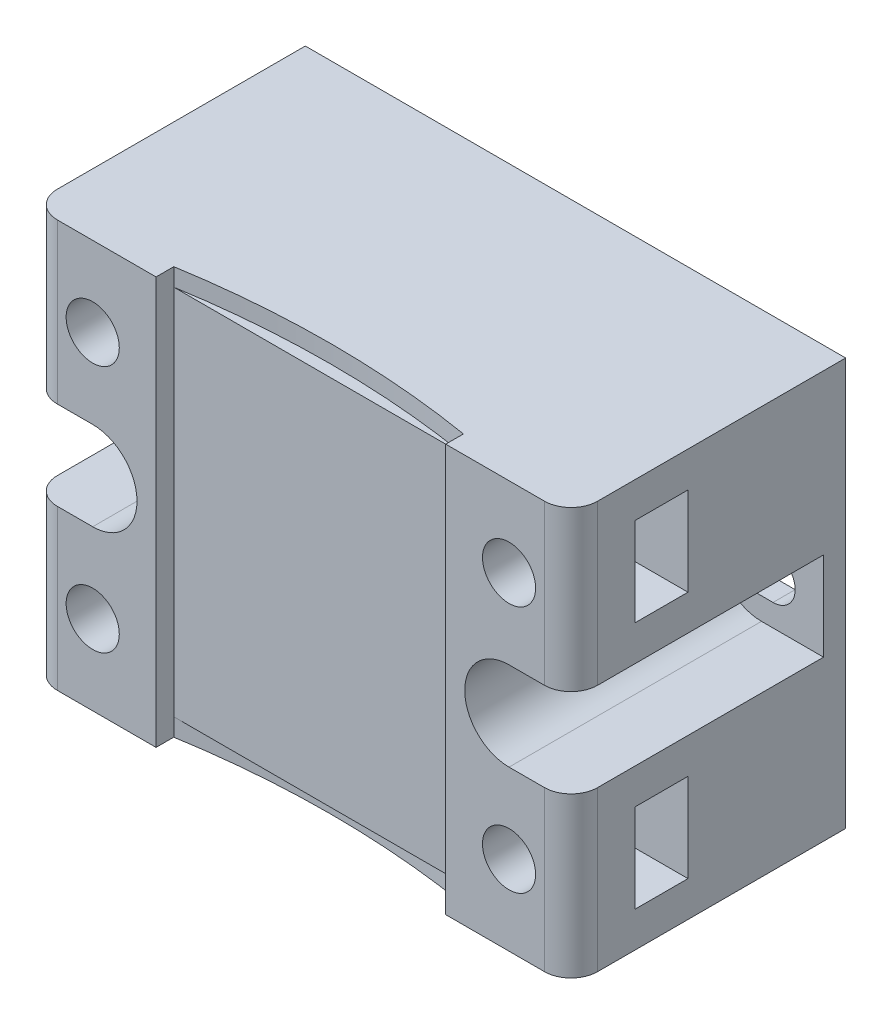
SolidWorks part; units mm, degrees
ref_plane "前视基准面" through (0, 0, 0) normal (0, 0, 1) x (1, 0, 0)
ref_plane "上视基准面" through (0, 0, 0) normal (0, 1, 0) x (1, 0, 0)
ref_plane "右视基准面" through (0, 0, 0) normal (1, 0, 0) x (0, 0, -1)
sketch "草图1" plane through (0, 0, 0) normal (0, 0, 1) x (1, 0, 0)
  line L1 (0, 0) -> (61, 0)
  line L2 (0, 0) -> (0, 46)
  line L3 (0, 46) -> (61, 46)
  line L4 (61, 0) -> (61, 46)
extrude "凸台-拉伸1" add sketch "草图1" along normal blind 31
sketch "草图2" plane through (0, 0, 31) normal (0, 0, 1) x (1, 0, 0)
  line L0 (30.5, 46) -> (30.5, 0)
  line L1 (61, 46) -> (0, 46) construction
  line L2 (0, 0) -> (61, 0) construction
  line L3 (30.5, 23) -> (12, 23)
  line L4 (12, 23) -> (7, 23)
  line L5 (7, 28) -> (0, 28)
  line L6 (0, 46) -> (61, 46)
  line L7 (0, 46) -> (0, 0)
  line L8 (0, 0) -> (61, 0)
  line L9 (61, 46) -> (61, 0)
  line L10 (0, 28) -> (0, 18)
  line L11 (0, 18) -> (7, 18)
  line L12 (61, 18) -> (54, 18)
  line L13 (54, 28) -> (61, 28)
  circle A0 centre (7, 23) radius 5
  circle A1 centre (54, 23) radius 5
  dimension "D1" = 10
extrude "切除-拉伸1" cut sketch "草图2" against normal blind 28.5
sketch "草图3" plane through (0, 0, 2.5) normal (0, 0, 1) x (1, 0, 0)
  line L0 (0, 23) -> (5.7, 23)
  line L1 (0, 28) -> (0, 18) construction
  circle A0 centre (5.7, 23) radius 2.5
  dimension "D1" = 5
extrude "切除-拉伸2" cut sketch "草图3" against normal blind 28.5
sketch "草图4" plane through (0, 0, 2.5) normal (0, 0, 1) x (1, 0, 0)
  line L3 (53.3, 25.5) -> (55.3, 25.5)
  line L4 (53.3, 20.5) -> (55.3, 20.5)
  arc A0 (55.3, 20.5) -> (55.3, 25.5) centre (55.3, 23) ccw
  arc A1 (53.3, 25.5) -> (53.3, 20.5) centre (53.3, 23) ccw
  dimension "D1" = 5
  dimension "D2" = 5
extrude "切除-拉伸3" cut sketch "草图4" against normal blind 28.5
sketch "草图5" plane through (0, 0, 0) normal (0, -1, 0) x (1, 0, 0)
  line L0 (30.5, 31) -> (46.85, 31)
  line L1 (0, 31) -> (61, 31) construction
  line L2 (46.85, 31) -> (46.85, 29)
  line L3 (46.85, 29) -> (14.15, 29)
  line L4 (14.15, 29) -> (14.15, 31)
  line L5 (14.15, 31) -> (30.5, 31)
extrude "切除-拉伸4" cut sketch "草图5" against normal blind 68.5
sketch "草图6" plane through (0, 0, 0) normal (0, -1, 0) x (1, 0, 0)
  line L0 (14.15, 29) -> (46.85, 29)
  arc A0 (14.15, 29) -> (46.85, 29) centre (30.5, 127.6543) ccw
extrude "切除-拉伸5" cut sketch "草图6" against normal blind 2
sketch "草图7" plane through (0, 46, 0) normal (0, 1, 0) x (1, 0, 0)
  line L1 (14.15, -29) -> (46.85, -29)
  line L2 (14.15, -29) -> (46.85, -29)
  arc A1 (46.85, -29) -> (14.15, -29) centre (30.5, -127.6543) ccw
  arc A2 (46.85, -29) -> (14.15, -29) centre (30.5, -127.6543) ccw
  dimension "D1" = 0
extrude "切除-拉伸6" cut sketch "草图7" against normal blind 2
sketch "草图8" plane through (0, 0, 31) normal (0, 0, 1) x (1, 0, 0)
  line L0 (0, 23) -> (12, 23)
  line L1 (0, 46) -> (7, 46)
  line L2 (0, 46) -> (0, 37)
  line L3 (0, 37) -> (7, 37)
  line L4 (7, 46) -> (7, 37)
  line L5 (0, 28) -> (0, 18) construction
  line L6 (30.5, 46) -> (30.5, 3.357)
  line L7 (46.85, 46) -> (14.15, 46) construction
  circle A0 centre (7, 37) radius 3
  arc A1 (7, 18) -> (7, 28) centre (7, 23) ccw construction
  circle A2 centre (7, 9) radius 3
  circle A3 centre (54, 9) radius 3
  circle A4 centre (54, 37) radius 3
  dimension "D1" = 6
extrude "切除-拉伸7" cut sketch "草图8" against normal blind 7.2 contours L3 A0 L4 | L4 A0 L3 | A2 | A3 | A4
sketch "草图9" plane through (0, 0, 0) normal (-1, 0, 0) x (0, 0, 1)
  line L0 (31, 37) -> (23.8, 37)
  line L1 (31, 46) -> (31, 28) construction
  line L2 (23.8, 37) -> (23.8, 46)
  line L3 (31, 46) -> (0, 46) construction
  line L4 (23.8, 46) -> (23.8, 42)
  line L5 (23.8, 42) -> (23.8, 32)
  line L6 (23.8, 32) -> (17.8, 32)
  line L7 (17.8, 32) -> (17.8, 41.5)
  line L8 (23.8, 42) -> (17.8, 42)
  line L9 (17.8, 42) -> (17.8, 41.5)
  line L10 (31, 23) -> (2.5, 23)
  line L11 (31, 18) -> (31, 28) construction
  line L12 (2.5, 28) -> (2.5, 18) construction
  line L13 (17.8, 4) -> (17.8, 4.5)
  line L14 (17.8, 14) -> (17.8, 4.5)
  line L15 (23.8, 4) -> (17.8, 4)
  line L16 (23.8, 4) -> (23.8, 14)
  line L17 (23.8, 14) -> (17.8, 14)
extrude "切除-拉伸8" cut sketch "草图9" against normal blind 10 contours L8 L9 L7 L6 L5 L2 | L16 L17 L14 L13 L15
sketch "草图10" plane through (61, 0, 0) normal (1, 0, 0) x (0, 0, -1)
  line L0 (-23.8, 4) -> (-23.8, 9) construction
  line L1 (-23.8, 9) -> (-23.8, 14) construction
  line L2 (-23.8, 14) -> (-17.8, 14) construction
  line L3 (-17.8, 14) -> (-17.8, 4) construction
  line L4 (-17.8, 4) -> (-23.8, 4) construction
  line L5 (-23.8, 42) -> (-17.8, 42) construction
  line L6 (-17.8, 42) -> (-17.8, 32) construction
  line L7 (-17.8, 32) -> (-23.8, 32) construction
  line L8 (-23.8, 32) -> (-23.8, 37) construction
  line L9 (-23.8, 37) -> (-23.8, 42) construction
  line L10 (-23.8, 4) -> (-23.8, 9)
  line L11 (-23.8, 9) -> (-23.8, 14)
  line L12 (-23.8, 14) -> (-17.8, 14)
  line L13 (-17.8, 14) -> (-17.8, 4)
  line L14 (-17.8, 4) -> (-23.8, 4)
  line L15 (-23.8, 42) -> (-17.8, 42)
  line L16 (-17.8, 42) -> (-17.8, 32)
  line L17 (-17.8, 32) -> (-23.8, 32)
  line L18 (-23.8, 32) -> (-23.8, 37)
  line L19 (-23.8, 37) -> (-23.8, 42)
extrude "切除-拉伸9" cut sketch "草图10" against normal blind 10
fillet "圆角1" radius 3 4 edges at (61, 9, 31) (61, 37, 31) (0, 9, 31) (0, 37, 31)
